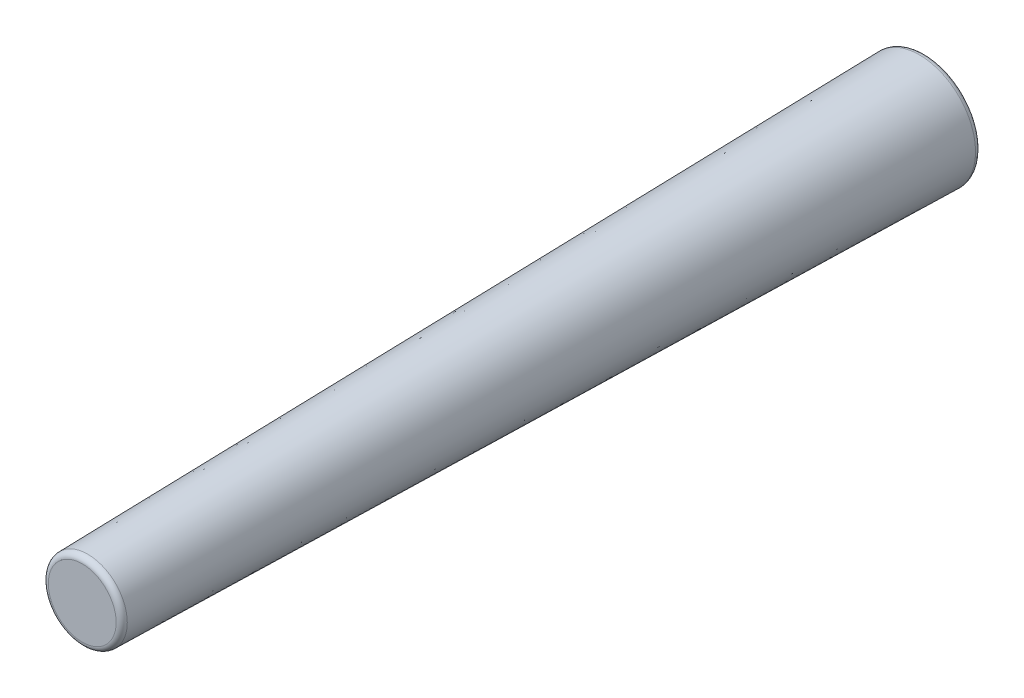
SolidWorks part; units mm, degrees
ref_plane "前视基准面" through (0, 0, 0) normal (0, 0, 1) x (1, 0, 0)
ref_plane "上视基准面" through (0, 0, 0) normal (0, 1, 0) x (1, 0, 0)
ref_plane "右视基准面" through (0, 0, 0) normal (1, 0, 0) x (0, 0, -1)
sketch "草图1" plane through (0, 0, 0) normal (0, 0, 1) x (1, 0, 0)
  circle A0 centre (0, 0) radius 1
  dimension "D1" = 2
extrude "凸台-拉伸1" add sketch "草图1" along normal blind 15 draft 1.14
fillet "圆角1" radius 0.1 2 edges at (1, 0, 0) (0.7015, 0, 15)
